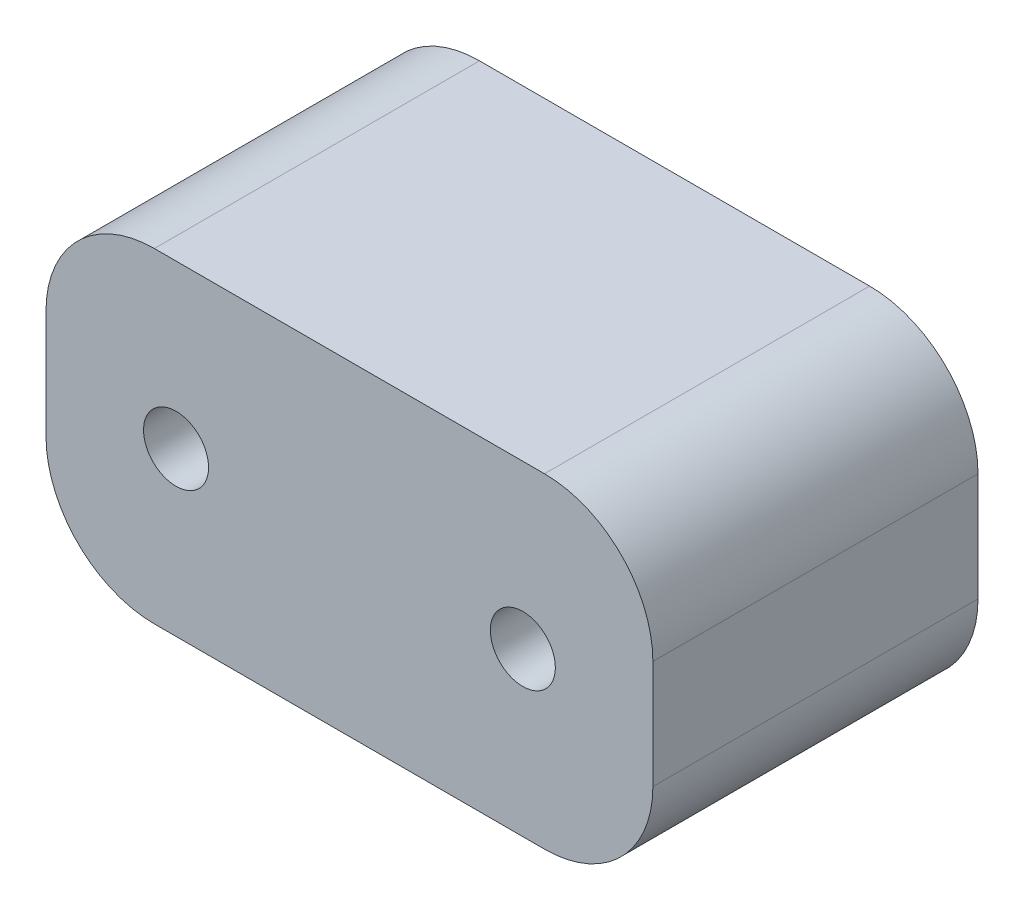
SolidWorks part; units mm, degrees
ref_plane "Plano frontal" through (0, 0, 0) normal (0, 0, 1) x (1, 0, 0)
ref_plane "Plano superior" through (0, 0, 0) normal (0, 1, 0) x (1, 0, 0)
ref_plane "Plano direito" through (0, 0, 0) normal (1, 0, 0) x (0, 0, -1)
sketch "Esboço1" plane through (0, 0, 0) normal (0, 0, 1) x (1, 0, 0)
  line L0 (-8, 0) -> (8, 0) construction
  line L1 (-14, -7.5) -> (14, -7.5)
  line L2 (-14, -7.5) -> (-14, 7.5)
  line L3 (-14, 7.5) -> (14, 7.5)
  line L4 (14, -7.5) -> (14, 7.5)
  line L5 (-14, -7.5) -> (14, 7.5) construction
  line L6 (-14, 7.5) -> (14, -7.5) construction
  circle A0 centre (-8, 0) radius 1.5
  circle A1 centre (8, 0) radius 1.5
  point P0 (0, 0)
  dimension "D1" = 3
  dimension "D2" = 15
  dimension "D3" = 16
  dimension "D4" = 6
extrude "Ressalto-extrusão1" add sketch "Esboço1" along normal blind 15
fillet "Filete1" radius 5 4 edges at (-14, 7.5, 7.5) (-14, -7.5, 7.5) (14, -7.5, 7.5) (14, 7.5, 7.5)
